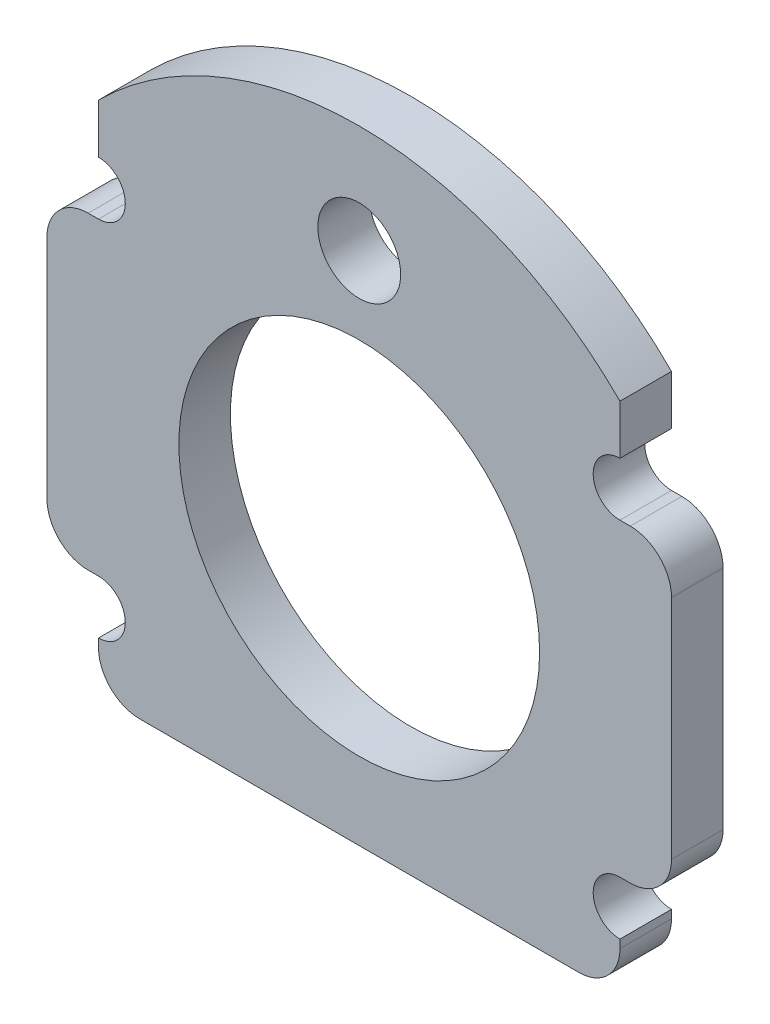
SolidWorks part; units mm, degrees
material "6061-T6 (SS)"
ref_plane "Front Plane" through (0, 0, 0) normal (0, 0, 1) x (1, 0, 0)
ref_plane "Top Plane" through (0, 0, 0) normal (0, 1, 0) x (1, 0, 0)
ref_plane "Right Plane" through (0, 0, 0) normal (1, 0, 0) x (0, 0, -1)
sketch "Sketch1" plane through (0, 0, 0) normal (0, 0, 1) x (1, 0, 0)
  line L0 (-19.2405, -9.525) -> (-19.2405, 9.525)
  line L1 (19.2405, -9.525) -> (19.2405, 9.525)
  line L2 (19.2405, 9.525) -> (16.0655, 9.525)
  line L3 (16.0655, 9.525) -> (16.0655, 15.875)
  line L4 (16.0655, 15.875) -> (-16.0655, 15.875)
  line L5 (-16.0655, 15.875) -> (-16.0655, 9.525)
  line L6 (-16.0655, 9.525) -> (-19.2405, 9.525)
  line L7 (-19.2405, -9.525) -> (-16.0655, -9.525)
  line L8 (-16.0655, -9.525) -> (-16.0655, -15.875)
  line L9 (-16.0655, -15.875) -> (16.0655, -15.875)
  line L10 (16.0655, -15.875) -> (16.0655, -9.525)
  line L11 (16.0655, -9.525) -> (19.2405, -9.525)
  line L12 (0, 0) -> (0, -15.875) construction
  line L13 (0, 0) -> (0, 15.875) construction
  circle A0 centre (0, 0) radius 11.1125
  point P6 (-19.2405, 0)
  point P9 (19.2405, 0)
  dimension "D1" = 22.225
  dimension "D2" = 32.131
  dimension "D3" = 3.175
  dimension "D4" = 6.35
  dimension "D5" = 31.75
extrude "Boss-Extrude1" add sketch "Sketch1" along normal blind 3.175
sketch "Sketch3" plane through (0, 0, 3.175) normal (0, 0, 1) x (1, 0, 0)
  line L2 (-16.0655, 15.875) -> (16.0655, 15.875)
  arc A1 (-16.0655, 15.875) -> (16.0655, 15.875) centre (0, -0.1905) cw
  dimension "D1" = 22.72
extrude "Boss-Extrude3" add sketch "Sketch3" against normal blind 3.175
sketch "Sketch4" plane through (0, 0, 0) normal (0, 0, -1) x (-1, 0, 0)
  line L0 (16.0655, 15.875) -> (-16.0655, 15.875) construction
  circle A0 centre (0, 15.875) radius 2.5527
  circle A1 centre (0, 15.875) radius 4.7625 construction
  dimension "D1" = 5.1054
  dimension "D2" = 9.525
extrude "Cut-Extrude2" cut sketch "Sketch4" against normal through all
fillet "Fillet1" radius 2.54 6 edges at (19.2405, 9.525, 1.5875) (19.2405, -9.525, 1.5875) (16.0655, -15.875, 1.5875) (-16.0655, -15.875, 1.5875) (-19.2405, -9.525, 1.5875) (-19.2405, 9.525, 1.5875)
sketch "Sketch2" plane through (0, 0, 3.175) normal (0, 0, 1) x (1, 0, 0)
  line L0 (-16.0655, -9.525) -> (-16.0655, -13.335) construction
  line L1 (-19.2405, 0) -> (19.2405, 0) construction
  line L2 (-19.2405, 6.985) -> (-19.2405, -6.985) construction
  line L3 (19.2405, -6.985) -> (19.2405, 6.985) construction
  line L4 (0, 18.4277) -> (0, -15.875) construction
  line L6 (-13.5255, -15.875) -> (13.5255, -15.875) construction
  line L7 (-16.0655, -9.525) -> (-16.0655, -12.827)
  line L8 (16.0655, -9.525) -> (16.0655, -12.827)
  line L9 (-16.0655, 9.525) -> (-16.0655, 12.827)
  line L10 (16.0655, 9.525) -> (16.0655, 12.827)
  arc A0 (-16.0655, -9.525) -> (-16.0655, -12.827) centre (-16.0655, -11.176) cw
  arc A1 (16.0655, -9.525) -> (16.0655, -12.827) centre (16.0655, -11.176) ccw
  arc A2 (-16.0655, 9.525) -> (-16.0655, 12.827) centre (-16.0655, 11.176) ccw
  arc A3 (16.0655, 9.525) -> (16.0655, 12.827) centre (16.0655, 11.176) cw
  circle A4 centre (0, 15.875) radius 2.5527 construction
  point P14 (-5.9045, 17.0858)
  point P15 (0, 0)
  point P27 (-6.7627, 15.875)
  point P28 (0, 0)
  point P29 (0, 18.4277)
  dimension "D1" = 3.302
extrude "Cut-Extrude1" cut sketch "Sketch2" against normal through all
